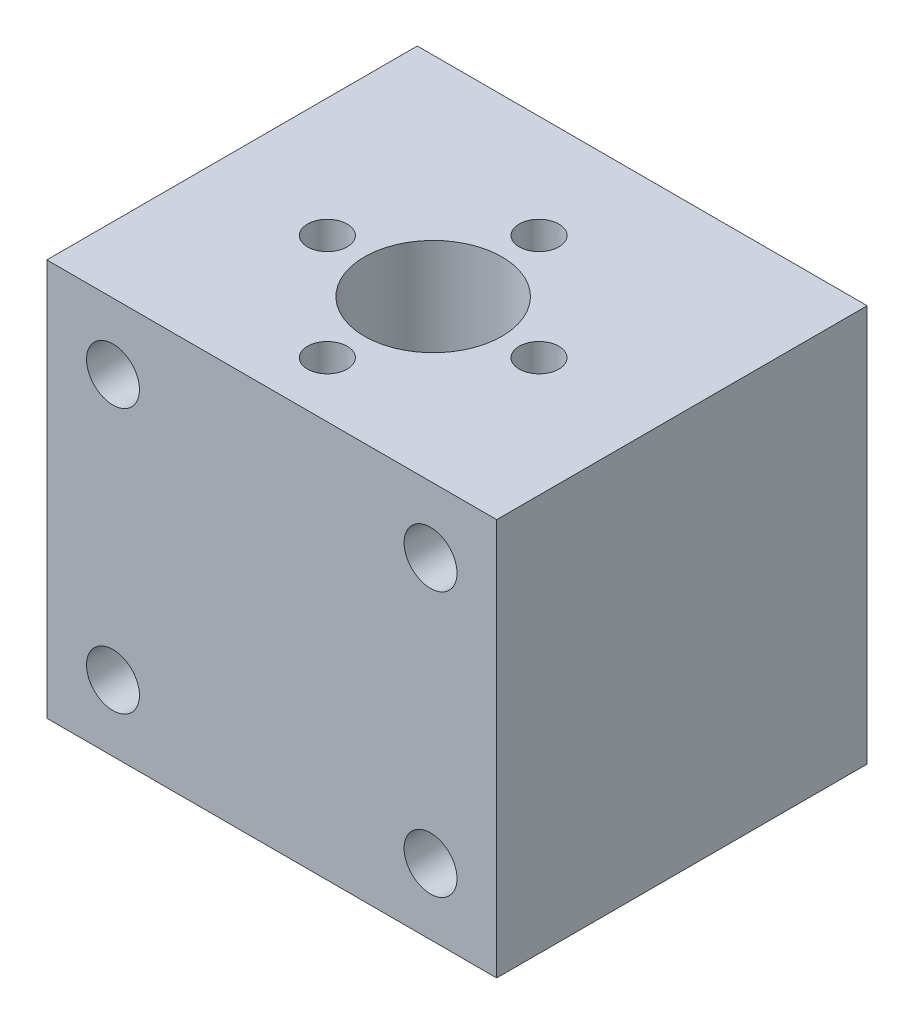
SolidWorks part; units mm, degrees
ref_plane "Front" through (0, 0, 0) normal (0, 0, 1) x (1, 0, 0)
ref_plane "Top" through (0, 0, 0) normal (0, 1, 0) x (1, 0, 0)
ref_plane "Right" through (0, 0, 0) normal (1, 0, 0) x (0, 0, -1)
sketch "草图1" plane through (0, 0, 0) normal (0, 0, 1) x (1, 0, 0)
  line L1 (-16.312, 9.8601) -> (17.688, 9.8601)
  line L2 (-16.312, 9.8601) -> (-16.312, -20.1399)
  line L3 (-16.312, -20.1399) -> (17.688, -20.1399)
  line L4 (17.688, 9.8601) -> (17.688, -20.1399)
  dimension "D1" = 34
  dimension "D2" = 30
extrude "凸台-拉伸1" add sketch "草图1" against normal blind 28
sketch "草图2" plane through (0, 0, 0) normal (0, 0, 1) x (1, 0, 0)
  circle A0 centre (-11.312, 4.8601) radius 2
  circle A1 centre (12.688, 4.8601) radius 2
  circle A2 centre (12.688, -15.1399) radius 2
  circle A3 centre (-11.312, -15.1399) radius 2
  point P0 (0, 0)
  dimension "D5" = 4
  dimension "D6" = 4
  dimension "D7" = 4
  dimension "D8" = 4
extrude "切除-拉伸1" cut sketch "草图2" against normal blind 7
sketch "草图3" plane through (0, 9.8601, 0) normal (0, 1, 0) x (1, 0, 0)
  line L0 (0.688, 0) -> (0.688, 7)
  line L1 (17.688, 0) -> (-16.312, 0) construction
  line L2 (17.688, 28) -> (-16.312, 28) construction
  line L3 (-52.5756, 12.2) -> (-4.512, 12.2)
  line L4 (0.688, 17.4) -> (0.688, 28)
  line L5 (5.888, 12.2) -> (51.93, 12.2)
  circle A0 centre (0.688, 12.2) radius 5.2
  dimension "D2" = 10.4
  dimension "D1" = 15.8
extrude "切除-拉伸3" cut sketch "草图3" against normal through all contours A0
sketch "草图5" plane through (0, 9.8601, 0) normal (0, 1, 0) x (1, 0, 0)
  circle A1 centre (0.688, 4.2) radius 1.5
  circle A2 centre (8.688, 12.2) radius 1.5
  circle A3 centre (0.688, 20.2) radius 1.5
  circle A4 centre (-7.312, 12.2) radius 1.5
  dimension "D2" = 3
  dimension "D3" = 3
  dimension "D4" = 3
  dimension "D5" = 3
extrude "切除-拉伸4" cut sketch "草图5" against normal blind 7
